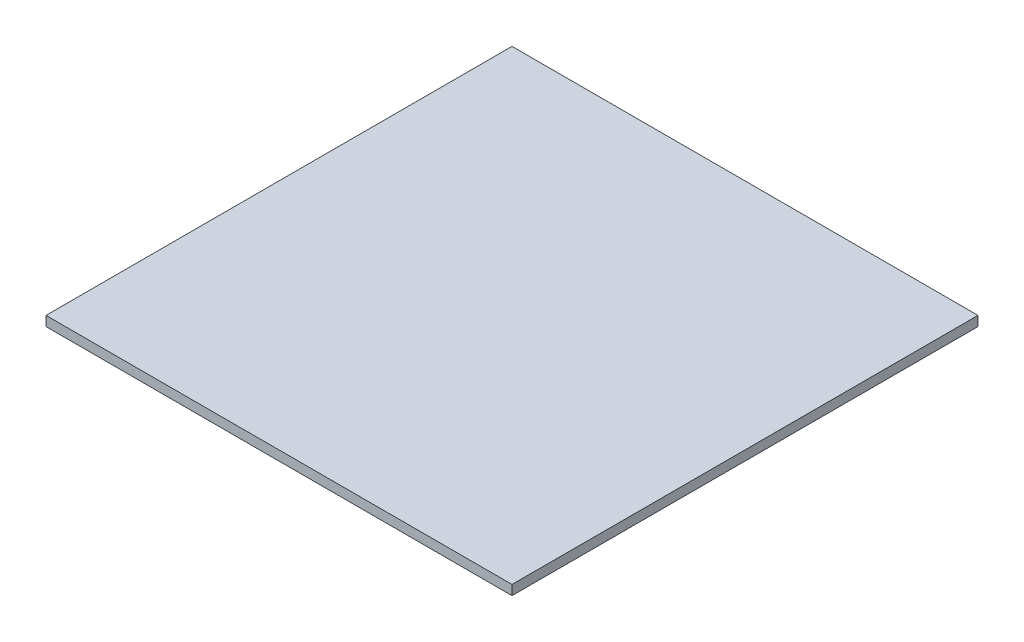
SolidWorks part; units mm, degrees
material "ABS PC"
ref_plane "Front Plane" through (0, 0, 0) normal (0, 0, 1) x (1, 0, 0)
ref_plane "Top Plane" through (0, 0, 0) normal (0, 1, 0) x (1, 0, 0)
ref_plane "Right Plane" through (0, 0, 0) normal (1, 0, 0) x (0, 0, -1)
sketch "Sketch1" plane through (0, 180.7471, 0) normal (0, 1, 0) x (1, 0, 0)
  line L0 (-143.7028, 148.529) -> (-143.7028, -91.471)
  line L1 (-143.7028, -91.471) -> (96.2972, -91.471)
  line L2 (96.2972, -91.471) -> (96.2972, 148.529)
  line L3 (96.2972, 148.529) -> (-143.7028, 148.529)
extrude "Boss-Extrude1" add sketch "Sketch1" along normal blind 5
sketch "Sketch2" plane through (0, 180.7471, 0) normal (0, -1, 0) x (1, 0, 0)
  circle A0 centre (-138.7028, 86.471) radius 3
  circle A1 centre (91.2972, 86.471) radius 3
  circle A2 centre (91.2972, -143.529) radius 3
  circle A3 centre (-138.7028, -143.529) radius 3
  dimension "D1" = 6
extrude "Cut-Extrude1" cut sketch "Sketch2" against normal blind 2
